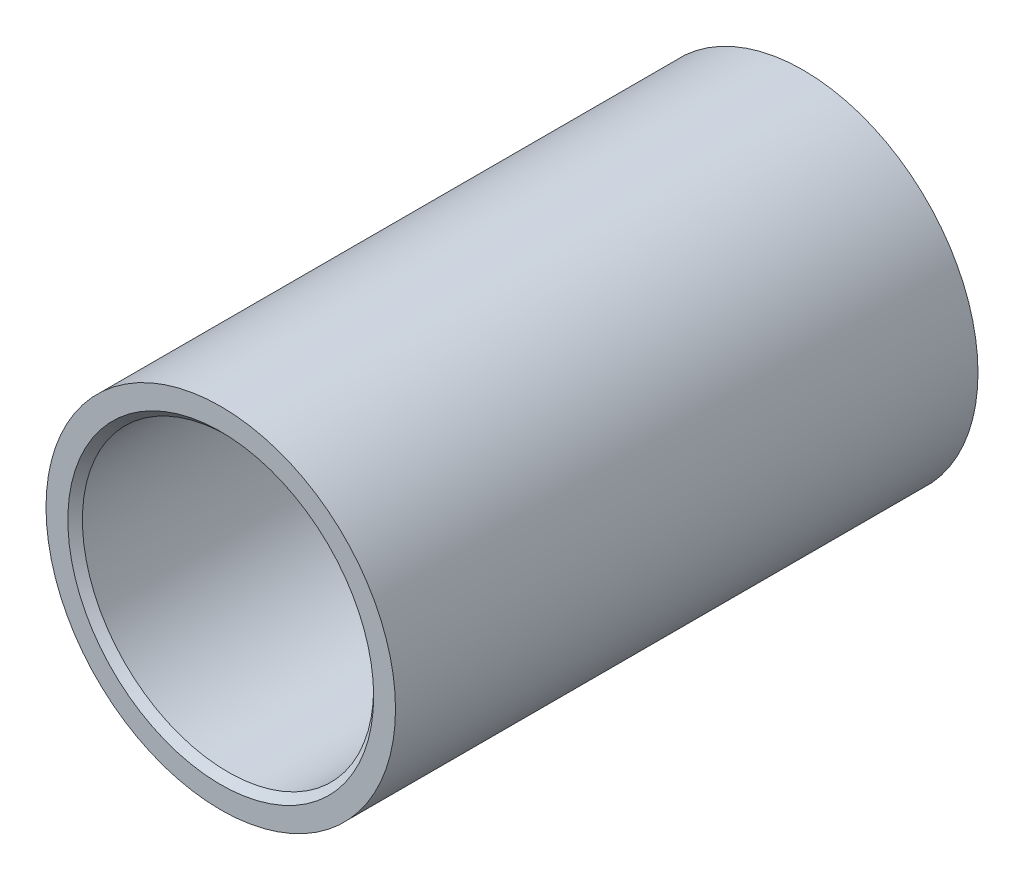
SolidWorks part; units mm, degrees
material "Plain Carbon Steel"
ref_plane "Front Plane" through (0, 0, 0) normal (0, 0, 1) x (1, 0, 0)
ref_plane "Top Plane" through (0, 0, 0) normal (0, 1, 0) x (1, 0, 0)
ref_plane "Right Plane" through (0, 0, 0) normal (1, 0, 0) x (0, 0, -1)
sketch "Sketch1" plane through (0, 0, 0) normal (0, 0, 1) x (1, 0, 0)
  circle A0 centre (0, 0) radius 19.05
  circle A1 centre (0, 0) radius 13.4938
  dimension "D1" = 38.1
  dimension "D2" = 26.9875
extrude "Boss-Extrude1" add sketch "Sketch1" along normal blind 31.75
sketch "Sketch2" plane through (0, 0, 31.75) normal (0, 0, 1) x (1, 0, 0)
  circle A0 centre (0, 0) radius 15.875
  dimension "D1" = 31.75
extrude "Cut-Extrude1" cut sketch "Sketch2" against normal blind 26.9875
mirror "Mirror1" about plane through (0, 0, 0) normal (0, 0, 1) of bodies 104
chamfer "Chamfer1" distance 0.7937 angle 45 2 edges at (15.875, 0, -31.75) (15.875, 0, 31.75)
